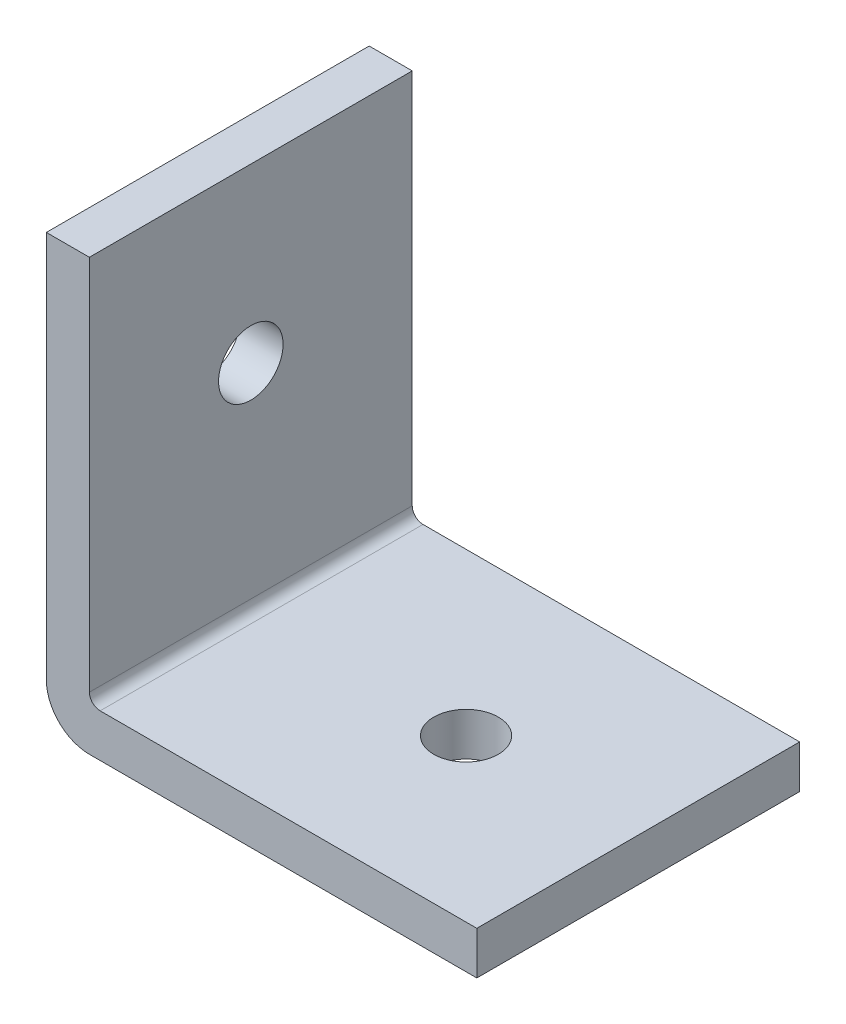
SolidWorks part; units mm, degrees
ref_plane "Front" through (0, 0, 0) normal (0, 0, 1) x (1, 0, 0)
ref_plane "Top" through (0, 0, 0) normal (0, 1, 0) x (1, 0, 0)
ref_plane "Right" through (0, 0, 0) normal (1, 0, 0) x (0, 0, -1)
sketch "Sketch1" plane through (0, 0, 0) normal (0, 0, 1) x (1, 0, 0)
  line L0 (0, 2) -> (0, 20)
  line L1 (0, 20) -> (2, 20)
  line L2 (2, 20) -> (2, 2.5)
  line L3 (2.5, 2) -> (20, 2)
  line L4 (20, 2) -> (20, 0)
  line L5 (20, 0) -> (2, 0)
  arc A0 (0, 2) -> (2, 0) centre (2, 2) ccw
  arc A1 (2.5, 2) -> (2, 2.5) centre (2.5, 2.5) cw
  point P9 (0, 0)
  point P12 (2, 2)
  dimension "D5" = 2
  dimension "D6" = 0.5
  dimension "D1" = 2
  dimension "D2" = 2
  dimension "D3" = 18
  dimension "D4" = 18
extrude "Boss-Extrude1" add sketch "Sketch1" along normal blind 15
ref_plane "Plane1" through (2, 0, 0) normal (1, 0, 0) x (0, 0, -1)
ref_plane "Plane2" through (0, 2, 0) normal (0, 1, 0) x (1, 0, 0)
sketch "Sketch3" plane through (0, 2, 0) normal (0, 1, 0) x (1, 0, 0)
  line L0 (20, 0) -> (2.5, 0) construction
  line L1 (20, -15) -> (20, 0) construction
  circle A0 centre (12, -7.5) radius 1.5
  dimension "D1" = 3
  dimension "D2" = 7.5
  dimension "D3" = 8
extrude "Cut-Extrude2" cut sketch "Sketch3" against normal through all contours A0
sketch "Sketch4" plane through (2, 0, 0) normal (1, 0, 0) x (0, 0, -1)
  line L0 (-15, 2.5) -> (-15, 20) construction
  line L2 (-15, 20) -> (0, 20) construction
  circle A0 centre (-7.5, 12) radius 1.5
  dimension "D1" = 3
  dimension "D2" = 7.5
  dimension "D3" = 8
extrude "Cut-Extrude3" cut sketch "Sketch4" against normal through all contours A0
